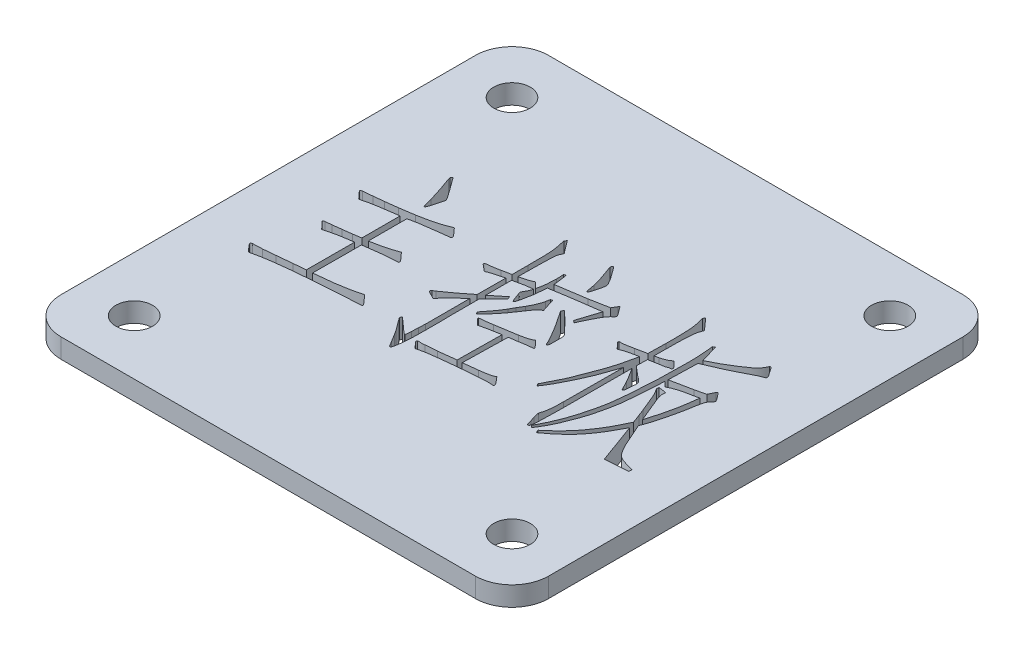
SolidWorks part; units mm, degrees
ref_plane "前视基准面" through (0, 0, 0) normal (0, 0, 1) x (1, 0, 0)
ref_plane "上视基准面" through (0, 0, 0) normal (0, 1, 0) x (1, 0, 0)
ref_plane "右视基准面" through (0, 0, 0) normal (1, 0, 0) x (0, 0, -1)
sketch "草图1" plane through (0, 0, 0) normal (0, 1, 0) x (1, 0, 0)
  line L1 (-20, -20) -> (20, -20)
  line L2 (-20, -20) -> (-20, 20)
  line L3 (-20, 20) -> (20, 20)
  line L4 (20, -20) -> (20, 20)
  line L5 (-20, -20) -> (20, 20) construction
  line L6 (-20, 20) -> (20, -20) construction
  point P0 (0, 0)
  dimension "D1" = 40
  dimension "D2" = 40
extrude "凸台-拉伸1" add sketch "草图1" along normal blind 1.6
sketch "草图2" plane through (0, 1.6, 0) normal (0, 1, 0) x (1, 0, 0)
  circle A0 centre (-15.5, 15.5) radius 1.5
  circle A1 centre (15.5, 15.5) radius 1.5
  circle A2 centre (15.5, -15.5) radius 1.5
  circle A3 centre (-15.5, -15.5) radius 1.5
  dimension "D1" = 15.5
  dimension "D2" = 15.5
  dimension "D3" = 15.5
  dimension "D4" = 15.5
  dimension "D5" = 15.5
  dimension "D6" = 15.5
  dimension "D8" = 15.5
  dimension "D9" = 3
  dimension "D10" = 3
  dimension "D11" = 3
  dimension "D12" = 3
  dimension "D7" = 15.5
extrude "切除-拉伸1" cut sketch "草图2" against normal through all
sketch "草图3" plane through (0, 1.6, 0) normal (0, 1, 0) x (1, 0, 0)
  text T0 "主控板" font "汉仪长仿宋体" height in points 42
extrude "切除-拉伸2" cut sketch "草图3" against normal blind 1.6
fillet "圆角1" radius 3 4 edges at (-20, 0.8, -20) (-20, 0.8, 20) (20, 0.8, 20) (20, 0.8, -20)
